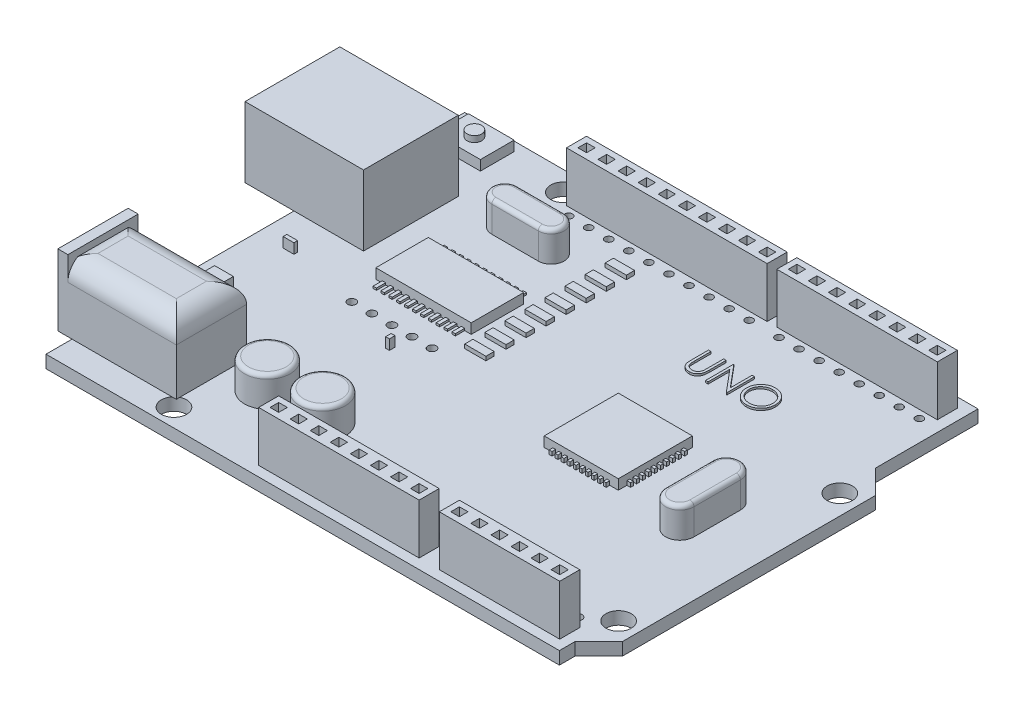
SolidWorks part; units mm, degrees
ref_plane "Front Plane" through (0, 0, 0) normal (0, 0, 1) x (1, 0, 0)
ref_plane "Top Plane" through (0, 0, 0) normal (0, 1, 0) x (1, 0, 0)
ref_plane "Right Plane" through (0, 0, 0) normal (1, 0, 0) x (0, 0, -1)
sketch "Sketch2" plane through (0, 0, 0) normal (0, 1, 0) x (1, 0, 0)
  line L0 (0, 0) -> (65, 0)
  line L1 (0, 0) -> (0, -53)
  line L2 (65, 0) -> (65, -13)
  line L3 (0, -53) -> (65, -53)
  line L4 (65, -13) -> (68, -16)
  line L5 (68, -16) -> (68, -48)
  line L6 (68, -48) -> (65, -51)
  line L7 (65, -51) -> (65, -53)
  circle A0 centre (15, -2.5) radius 1.6
  circle A1 centre (65.5, -18) radius 1.6
  circle A2 centre (65.5, -46) radius 1.6
  circle A3 centre (13.9, -50.7) radius 1.6
  dimension "D8" = 3.2
  dimension "D9" = 15
  dimension "D12" = 35
  dimension "D13" = 50.5
  dimension "D14" = 1.1
  dimension "D15" = 4.7
  dimension "D1" = 65
  dimension "D2" = 53
  dimension "D3" = 37
  dimension "D4" = 40
  dimension "D5" = 2
  dimension "D6" = 5
  dimension "D7" = 68
  dimension "D10" = 65.5
  dimension "D11" = 7
extrude "Boss-Extrude1" add sketch "Sketch2" along normal blind 1.6
sketch "Sketch3" plane through (0, 1.6, 0) normal (0, 1, 0) x (1, 0, 0)
  line L0 (-6.2, -9.6) -> (8.8, -9.6)
  line L1 (-6.2, -9.6) -> (-6.2, -21.6)
  line L2 (8.8, -9.6) -> (8.8, -21.6)
  line L3 (-6.2, -21.6) -> (8.8, -21.6)
  line L4 (65, 0) -> (0, 0) construction
  line L5 (0, 0) -> (0, -53) construction
  dimension "D1" = 9.6
  dimension "D2" = 12
  dimension "D3" = 15
  dimension "D4" = 6.2
extrude "Boss-Extrude2" add sketch "Sketch3" along normal blind 8.9
sketch "Sketch5" plane through (0, 1.6, 0) normal (0, 1, 0) x (1, 0, 0)
  line L0 (0, 0) -> (0, -9.6) construction
  line L1 (7.4283, -5.4315) -> (1.6434, -5.4315)
  line L2 (7.4283, -5.4315) -> (7.4283, -1.1571)
  line L3 (7.4283, -1.1571) -> (1.6434, -1.1571)
  line L4 (1.6434, -5.4315) -> (1.6434, -1.1571)
  line L5 (7.4283, -5.4315) -> (1.6434, -1.1571) construction
  line L6 (7.4283, -1.1571) -> (1.6434, -5.4315) construction
  line L7 (65, 0) -> (0, 0) construction
  point P0 (4.5358, -3.2943)
  dimension "D1" = 4.2744
  dimension "D2" = 5.7848
  dimension "D3" = 1.6434
  dimension "D4" = 1.1571
extrude "Boss-Extrude3" add sketch "Sketch5" along normal blind 1.27
sketch "Sketch6" plane through (0, 2.87, 0) normal (0, 1, 0) x (1, 0, 0)
  line L0 (1.6434, -1.1571) -> (7.4283, -5.4315) construction
  circle A0 centre (4.5358, -3.2943) radius 0.9278
  dimension "D1" = 1.8555
extrude "Boss-Extrude4" add sketch "Sketch6" along normal blind 0.762
sketch "Sketch7" plane through (0, 1.6, 0) normal (0, 1, 0) x (1, 0, 0)
  line L0 (0, -21.6) -> (0, -53) construction
  line L1 (-1.8, -40.8) -> (13.2, -40.8)
  line L2 (-1.8, -40.8) -> (-1.8, -49.7)
  line L3 (-1.8, -49.7) -> (13.2, -49.7)
  line L4 (13.2, -40.8) -> (13.2, -49.7)
  line L5 (-1.8, -40.8) -> (13.2, -49.7) construction
  line L6 (-1.8, -49.7) -> (13.2, -40.8) construction
  line L7 (0, -53) -> (65, -53) construction
  point P0 (5.7, -45.25)
  dimension "D1" = 8.9
  dimension "D2" = 1.8
  dimension "D3" = 15
  dimension "D4" = 3.3
extrude "Boss-Extrude5" add sketch "Sketch7" along normal blind 8.5
fillet "Fillet1" radius 2.54 4 edges at (5.7, 10.1, 49.7) (-1.8, 10.1, 45.25) (5.7, 10.1, 40.8) (13.2, 10.1, 45.25)
sketch "Sketch8" plane through (-1.8, 0, 0) normal (-1, 0, 0) x (0, 0, 1)
  line L0 (49.7, 1.6) -> (53, 1.6) construction
  line L1 (49.7, 1.6) -> (40.8, 1.6)
  line L2 (49.7, 1.6) -> (49.7, 10.6)
  line L3 (49.7, 10.6) -> (40.8, 10.6)
  line L4 (40.8, 1.6) -> (40.8, 10.6)
  line L5 (49.7, 1.6) -> (40.8, 10.6) construction
  line L6 (49.7, 10.6) -> (40.8, 1.6) construction
  line L7 (49.7, 7.56) -> (49.7, 1.6) construction
  line L9 (40.8, 7.56) -> (40.8, 1.6) construction
  point P0 (45.25, 6.1)
  dimension "D1" = 9
extrude "Boss-Extrude6" add sketch "Sketch8" against normal blind 1.27
sketch "Sketch9" plane through (-1.8, 0, 0) normal (-1, 0, 0) x (0, 0, 1)
  line L0 (45.25, 10.6) -> (45.25, 1.6) construction
  line L1 (49.7, 10.6) -> (40.8, 10.6) construction
  line L2 (40.8, 1.6) -> (49.7, 1.6) construction
  circle A0 centre (45.25, 6.1) radius 3
  dimension "D1" = 6
extrude "Cut-Extrude2" cut sketch "Sketch9" against normal blind 8.89
sketch "Sketch11" plane through (0, 1.6, 0) normal (0, 1, 0) x (1, 0, 0)
  line L0 (15.083, -10) -> (20.9573, -10) construction
  line L1 (15.083, -8.3682) -> (20.9573, -8.3682)
  line L2 (15.083, -11.6318) -> (20.9573, -11.6318)
  line L3 (59.2606, -32.0122) -> (59.2606, -26.1378) construction
  line L4 (57.4656, -32.0122) -> (57.4656, -26.1378)
  line L5 (61.0555, -32.0122) -> (61.0555, -26.1378)
  line L6 (0, -53) -> (65, -53) construction
  line L7 (0, -21.6) -> (0, -40.8) construction
  line L8 (65, 0) -> (0, 0) construction
  circle A0 centre (18.0202, -43) radius 2.8915
  circle A1 centre (25.0202, -43) radius 2.8915
  arc A2 (15.083, -8.3682) -> (15.083, -11.6318) centre (15.083, -10) ccw
  arc A3 (20.9573, -11.6318) -> (20.9573, -8.3682) centre (20.9573, -10) ccw
  arc A4 (57.4656, -32.0122) -> (61.0555, -32.0122) centre (59.2606, -32.0122) ccw
  arc A5 (61.0555, -26.1378) -> (57.4656, -26.1378) centre (59.2606, -26.1378) ccw
  point P6 (18.0202, -10)
  point P11 (59.2606, -29.075)
  dimension "D1" = 7
  dimension "D2" = 5.783
  dimension "D4" = 18.0202
  dimension "D6" = 1.6318
  dimension "14" = 10
  dimension "D5" = 5.8744
  dimension "D7" = 10
  dimension "D8" = 18.0202
extrude "Boss-Extrude8" add sketch "Sketch11" along normal blind 3.81
fillet "Fillet2" radius 0.508 1 edges at (18.0202, 5.41, 45.8915)
fillet "Fillet3" radius 0.508 9 edges at (59.2606, 5.41, 24.3429) (61.0555, 5.41, 29.075) (59.2606, 5.41, 33.8071) (18.0202, 5.41, 8.3682) (22.5891, 5.41, 10) (18.0202, 5.41, 11.6318) (57.4656, 5.41, 29.075) (13.4512, 5.41, 10) (25.0202, 5.41, 45.8915)
sketch "Sketch12" plane through (0, 1.6, 0) normal (0, 1, 0) x (1, 0, 0)
  line L0 (39.53, -1.23) -> (39.53, -3.77) construction
  line L1 (16.67, -1.23) -> (42.07, -1.23)
  line L2 (16.67, -1.23) -> (16.67, -3.77)
  line L3 (16.67, -3.77) -> (42.07, -3.77)
  line L4 (42.07, -1.23) -> (42.07, -3.77)
  line L5 (16.67, -1.23) -> (42.07, -3.77) construction
  line L6 (16.67, -3.77) -> (42.07, -1.23) construction
  line L7 (43.3, -1.23) -> (63.62, -1.23)
  line L8 (43.3, -1.23) -> (43.3, -3.77)
  line L9 (43.3, -3.77) -> (63.62, -3.77)
  line L10 (63.62, -1.23) -> (63.62, -3.77)
  line L11 (43.3, -1.23) -> (63.62, -3.77) construction
  line L12 (43.3, -3.77) -> (63.62, -1.23) construction
  line L13 (39.53, -1.23) -> (42.07, -3.77) construction
  line L14 (0, 0) -> (0, -9.6) construction
  line L15 (16.67, -2.5) -> (15, -2.5) construction
  line L17 (25.65, -49.19) -> (45.97, -49.19)
  line L18 (25.65, -49.19) -> (25.65, -51.73)
  line L19 (25.65, -51.73) -> (45.97, -51.73)
  line L20 (45.97, -49.19) -> (45.97, -51.73)
  line L21 (48.53, -49.19) -> (63.77, -49.19)
  line L22 (48.53, -49.19) -> (48.53, -51.73)
  line L23 (48.53, -51.73) -> (63.77, -51.73)
  line L24 (63.77, -49.19) -> (63.77, -51.73)
  line L25 (43.43, -49.19) -> (43.43, -51.73) construction
  line L26 (43.43, -51.73) -> (45.97, -49.19) construction
  line L27 (0, -49.7) -> (0, -53) construction
  line L28 (0, -53) -> (65, -53) construction
  line L29 (63.77, -49.19) -> (61.23, -51.73) construction
  line L30 (63.62, -1.23) -> (61.38, -3.77) construction
  circle A0 centre (15, -2.5) radius 1.6 construction
  point P0 (29.37, -2.5)
  point P5 (53.46, -2.5)
  point P14 (40.8, -2.5)
  point P27 (45.97, -50.46)
  point P28 (44.7, -50.46)
  point P35 (62.5, -50.46)
  point P37 (62.5, -2.5)
  dimension "D1" = 25.4
  dimension "D2" = 2.54
  dimension "D3" = 2.54
  dimension "D4" = 40.8
  dimension "D5" = 20.32
  dimension "D6" = 2.54
  dimension "D7" = 44.7
  dimension "D8" = 2.54
  dimension "D9" = 2.54
  dimension "D10" = 62.5
  dimension "D11" = 2.24
  dimension "D12" = 62.5
  dimension "D13" = 20.32
  dimension "D14" = 15.24
extrude "Boss-Extrude9" add sketch "Sketch12" along normal blind 6.35
sketch "Sketch13" plane through (0, 7.95, 0) normal (0, 1, 0) x (1, 0, 0)
  line L0 (19.9337, -3.0463) -> (19.9337, -1.9537)
  line L1 (18.4863, -3.0463) -> (17.3937, -3.0463)
  line L2 (18.4863, -3.0463) -> (18.4863, -1.9537)
  line L3 (18.4863, -1.9537) -> (17.3937, -1.9537)
  line L4 (17.3937, -3.0463) -> (17.3937, -1.9537)
  line L5 (18.4863, -3.0463) -> (17.3937, -1.9537) construction
  line L6 (18.4863, -1.9537) -> (17.3937, -3.0463) construction
  line L7 (21.0263, -1.9537) -> (19.9337, -1.9537)
  line L8 (21.0263, -3.0463) -> (19.9337, -3.0463)
  line L9 (21.0263, -3.0463) -> (21.0263, -1.9537)
  line L10 (22.4737, -3.0463) -> (22.4737, -1.9537)
  line L11 (23.5663, -1.9537) -> (22.4737, -1.9537)
  line L12 (23.5663, -3.0463) -> (22.4737, -3.0463)
  line L13 (23.5663, -3.0463) -> (23.5663, -1.9537)
  line L14 (25.0137, -3.0463) -> (25.0137, -1.9537)
  line L15 (26.1063, -1.9537) -> (25.0137, -1.9537)
  line L16 (26.1063, -3.0463) -> (25.0137, -3.0463)
  line L17 (26.1063, -3.0463) -> (26.1063, -1.9537)
  line L18 (27.5537, -3.0463) -> (27.5537, -1.9537)
  line L19 (28.6463, -1.9537) -> (27.5537, -1.9537)
  line L20 (28.6463, -3.0463) -> (27.5537, -3.0463)
  line L21 (28.6463, -3.0463) -> (28.6463, -1.9537)
  line L22 (30.0937, -3.0463) -> (30.0937, -1.9537)
  line L23 (31.1863, -1.9537) -> (30.0937, -1.9537)
  line L24 (31.1863, -3.0463) -> (30.0937, -3.0463)
  line L25 (31.1863, -3.0463) -> (31.1863, -1.9537)
  line L26 (32.6337, -3.0463) -> (32.6337, -1.9537)
  line L27 (33.7263, -1.9537) -> (32.6337, -1.9537)
  line L28 (33.7263, -3.0463) -> (32.6337, -3.0463)
  line L29 (33.7263, -3.0463) -> (33.7263, -1.9537)
  line L30 (35.1737, -3.0463) -> (35.1737, -1.9537)
  line L31 (36.2663, -1.9537) -> (35.1737, -1.9537)
  line L32 (36.2663, -3.0463) -> (35.1737, -3.0463)
  line L33 (36.2663, -3.0463) -> (36.2663, -1.9537)
  line L34 (16.67, -2.5) -> (17.94, -2.5) construction
  line L35 (16.67, -1.23) -> (16.67, -3.77) construction
  line L36 (42.07, -1.23) -> (43.3, -1.23) construction
  line L37 (43.3, -1.23) -> (42.685, -1.23) construction
  line L38 (42.685, -1.23) -> (42.685, 0) construction
  line L39 (65, 0) -> (0, 0) construction
  line L40 (44.0237, -3.0463) -> (44.0237, -1.9537)
  line L41 (44.0237, -3.0463) -> (45.1163, -3.0463)
  line L42 (44.0237, -1.9537) -> (45.1163, -1.9537)
  line L43 (49.1037, -3.0463) -> (49.1037, -1.9537)
  line L44 (49.1037, -3.0463) -> (50.1963, -3.0463)
  line L45 (49.1037, -1.9537) -> (50.1963, -1.9537)
  line L46 (50.1963, -3.0463) -> (50.1963, -1.9537)
  line L47 (51.6437, -3.0463) -> (51.6437, -1.9537)
  line L48 (51.6437, -3.0463) -> (52.7363, -3.0463)
  line L49 (51.6437, -1.9537) -> (52.7363, -1.9537)
  line L50 (52.7363, -3.0463) -> (52.7363, -1.9537)
  line L51 (54.1837, -3.0463) -> (54.1837, -1.9537)
  line L52 (54.1837, -3.0463) -> (55.2763, -3.0463)
  line L53 (54.1837, -1.9537) -> (55.2763, -1.9537)
  line L54 (55.2763, -3.0463) -> (55.2763, -1.9537)
  line L55 (56.7237, -3.0463) -> (56.7237, -1.9537)
  line L56 (56.7237, -3.0463) -> (57.8163, -3.0463)
  line L57 (56.7237, -1.9537) -> (57.8163, -1.9537)
  line L58 (57.8163, -3.0463) -> (57.8163, -1.9537)
  line L59 (59.2637, -3.0463) -> (59.2637, -1.9537)
  line L60 (59.2637, -3.0463) -> (60.3563, -3.0463)
  line L61 (59.2637, -1.9537) -> (60.3563, -1.9537)
  line L62 (60.3563, -3.0463) -> (60.3563, -1.9537)
  line L63 (61.8037, -3.0463) -> (61.8037, -1.9537)
  line L64 (61.8037, -3.0463) -> (62.8963, -3.0463)
  line L65 (61.8037, -1.9537) -> (62.8963, -1.9537)
  line L66 (62.8963, -3.0463) -> (62.8963, -1.9537)
  line L67 (45.1163, -3.0463) -> (45.1163, -1.9537)
  line L68 (46.5637, -3.0463) -> (46.5637, -1.9537)
  line L69 (46.5637, -3.0463) -> (47.6563, -3.0463)
  line L71 (46.5637, -1.9537) -> (47.6563, -1.9537)
  line L72 (47.6563, -3.0463) -> (47.6563, -1.9537)
  line L73 (41.6137, -49.9137) -> (42.7063, -49.9137)
  line L74 (41.6137, -49.9137) -> (41.6137, -51.0063)
  line L75 (41.6137, -51.0063) -> (42.7063, -51.0063)
  line L77 (26.3737, -49.9137) -> (27.4663, -49.9137)
  line L78 (26.3737, -49.9137) -> (26.3737, -51.0063)
  line L79 (26.3737, -51.0063) -> (27.4663, -51.0063)
  line L80 (27.4663, -49.9137) -> (27.4663, -51.0063)
  line L81 (26.3737, -50.46) -> (25.65, -50.46) construction
  line L82 (25.65, -49.19) -> (25.65, -51.73) construction
  line L83 (28.9137, -49.9137) -> (30.0063, -49.9137)
  line L84 (28.9137, -49.9137) -> (28.9137, -51.0063)
  line L85 (28.9137, -51.0063) -> (30.0063, -51.0063)
  line L86 (30.0063, -49.9137) -> (30.0063, -51.0063)
  line L87 (31.4537, -49.9137) -> (32.5463, -49.9137)
  line L88 (31.4537, -49.9137) -> (31.4537, -51.0063)
  line L89 (31.4537, -51.0063) -> (32.5463, -51.0063)
  line L90 (32.5463, -49.9137) -> (32.5463, -51.0063)
  line L91 (33.9937, -49.9137) -> (35.0863, -49.9137)
  line L92 (33.9937, -49.9137) -> (33.9937, -51.0063)
  line L93 (33.9937, -51.0063) -> (35.0863, -51.0063)
  line L94 (35.0863, -49.9137) -> (35.0863, -51.0063)
  line L95 (36.5337, -49.9137) -> (37.6263, -49.9137)
  line L96 (36.5337, -49.9137) -> (36.5337, -51.0063)
  line L97 (36.5337, -51.0063) -> (37.6263, -51.0063)
  line L98 (37.6263, -49.9137) -> (37.6263, -51.0063)
  line L99 (39.0737, -49.9137) -> (40.1663, -49.9137)
  line L100 (39.0737, -49.9137) -> (39.0737, -51.0063)
  line L101 (39.0737, -51.0063) -> (40.1663, -51.0063)
  line L102 (40.1663, -49.9137) -> (40.1663, -51.0063)
  line L103 (45.97, -51.73) -> (48.53, -51.73) construction
  line L104 (48.53, -51.73) -> (47.25, -51.73) construction
  line L105 (47.25, -51.73) -> (47.25, -53) construction
  line L106 (0, -53) -> (65, -53) construction
  line L107 (49.2537, -49.9137) -> (49.2537, -51.0063)
  line L108 (54.3337, -49.9137) -> (54.3337, -51.0063)
  line L109 (55.4263, -51.0063) -> (54.3337, -51.0063)
  line L110 (55.4263, -49.9137) -> (55.4263, -51.0063)
  line L111 (55.4263, -49.9137) -> (54.3337, -49.9137)
  line L112 (56.8737, -49.9137) -> (56.8737, -51.0063)
  line L113 (57.9663, -51.0063) -> (56.8737, -51.0063)
  line L114 (57.9663, -49.9137) -> (57.9663, -51.0063)
  line L115 (57.9663, -49.9137) -> (56.8737, -49.9137)
  line L116 (59.4137, -49.9137) -> (59.4137, -51.0063)
  line L117 (60.5063, -51.0063) -> (59.4137, -51.0063)
  line L118 (60.5063, -49.9137) -> (60.5063, -51.0063)
  line L119 (60.5063, -49.9137) -> (59.4137, -49.9137)
  line L120 (61.9537, -49.9137) -> (61.9537, -51.0063)
  line L121 (63.0463, -51.0063) -> (61.9537, -51.0063)
  line L122 (63.0463, -49.9137) -> (63.0463, -51.0063)
  line L123 (63.0463, -49.9137) -> (61.9537, -49.9137)
  line L124 (50.3463, -51.0063) -> (49.2537, -51.0063)
  line L125 (50.3463, -49.9137) -> (50.3463, -51.0063)
  line L126 (50.3463, -49.9137) -> (49.2537, -49.9137)
  line L127 (51.7937, -49.9137) -> (51.7937, -51.0063)
  line L128 (52.8863, -51.0063) -> (51.7937, -51.0063)
  line L129 (52.8863, -49.9137) -> (52.8863, -51.0063)
  line L130 (52.8863, -49.9137) -> (51.7937, -49.9137)
  line L132 (37.7137, -3.0463) -> (37.7137, -1.9537)
  line L133 (38.8063, -1.9537) -> (37.7137, -1.9537)
  line L134 (38.8063, -3.0463) -> (37.7137, -3.0463)
  line L135 (38.8063, -3.0463) -> (38.8063, -1.9537)
  line L136 (40.2537, -3.0463) -> (40.2537, -1.9537)
  line L137 (41.3463, -1.9537) -> (40.2537, -1.9537)
  line L138 (41.3463, -3.0463) -> (40.2537, -3.0463)
  line L139 (41.3463, -3.0463) -> (41.3463, -1.9537)
  line L140 (42.7063, -49.9137) -> (42.7063, -51.0063)
  line L141 (44.1537, -49.9137) -> (45.2463, -49.9137)
  line L142 (44.1537, -49.9137) -> (44.1537, -51.0063)
  line L143 (44.1537, -51.0063) -> (45.2463, -51.0063)
  line L144 (45.2463, -49.9137) -> (45.2463, -51.0063)
  point P0 (17.94, -2.5)
  point P84 (26.92, -51.0063)
  dimension "D2" = 2.54
  dimension "D3" = 1.0927
  dimension "D4" = 1.27
  dimension "D5" = 1.27
  dimension "D6" = 8
  dimension "D7" = 2.54
  dimension "D1" = 10
extrude "Cut-Extrude3" cut sketch "Sketch13" against normal blind 3.81
sketch "Sketch15" plane through (0, 1.6, 0) normal (0, 1, 0) x (1, 0, 0)
  line L0 (0, -53) -> (65, -53) construction
  line L1 (51.1538, -31.6917) -> (41.7703, -31.6917)
  line L2 (51.1538, -31.6917) -> (51.1538, -22.3083)
  line L3 (51.1538, -22.3083) -> (41.7703, -22.3083)
  line L4 (41.7703, -31.6917) -> (41.7703, -22.3083)
  line L5 (51.1538, -31.6917) -> (41.7703, -22.3083) construction
  line L6 (51.1538, -22.3083) -> (41.7703, -31.6917) construction
  line L7 (4.7493, -26.358) -> (3.3785, -26.358)
  line L8 (4.7493, -26.358) -> (4.7493, -25.8868)
  line L9 (4.7493, -25.8868) -> (3.3785, -25.8868)
  line L10 (3.3785, -26.358) -> (3.3785, -25.8868)
  line L11 (4.7493, -26.358) -> (3.3785, -25.8868) construction
  line L12 (4.7493, -25.8868) -> (3.3785, -26.358) construction
  line L13 (21.3282, -30.8535) -> (20.8488, -30.8535)
  line L14 (21.3282, -30.8535) -> (21.3282, -30.1486)
  line L15 (21.3282, -30.1486) -> (20.8488, -30.1486)
  line L16 (20.8488, -30.8535) -> (20.8488, -30.1486)
  line L17 (21.3282, -30.8535) -> (20.8488, -30.1486) construction
  line L18 (21.3282, -30.1486) -> (20.8488, -30.8535) construction
  line L19 (4.6108, -37.8097) -> (2.2268, -37.8097)
  line L20 (4.6108, -37.8097) -> (4.6108, -33.8836)
  line L21 (4.6108, -33.8836) -> (2.2268, -33.8836)
  line L22 (2.2268, -37.8097) -> (2.2268, -33.8836)
  line L23 (4.6108, -37.8097) -> (2.2268, -33.8836) construction
  line L24 (4.6108, -33.8836) -> (2.2268, -37.8097) construction
  line L25 (24.7492, -23.9138) -> (12.6715, -23.9138)
  line L26 (24.7492, -23.9138) -> (24.7492, -17.271)
  line L27 (24.7492, -17.271) -> (12.6715, -17.271)
  line L28 (12.6715, -23.9138) -> (12.6715, -17.271)
  line L29 (24.7492, -23.9138) -> (12.6715, -17.271) construction
  line L30 (24.7492, -17.271) -> (12.6715, -23.9138) construction
  line L31 (68, -48) -> (68, -16) construction
  line L32 (0, -21.6) -> (0, -40.8) construction
  line L34 (65, 0) -> (0, 0) construction
  point P0 (46.4621, -27)
  point P5 (4.0639, -26.1224)
  point P10 (21.0885, -30.501)
  point P15 (3.4188, -35.8466)
  point P20 (18.7104, -20.5924)
  dimension "D1" = 9.3835
  dimension "D2" = 12.0778
  dimension "D3" = 6.6428
  dimension "D4" = 26
  dimension "D5" = 21.5379
  dimension "D6" = 18.7104
  dimension "D7" = 20.5924
extrude "Boss-Extrude10" add sketch "Sketch15" along normal blind 1.27
sketch "Sketch16" plane through (0, 1.6, 0) normal (0, 1, 0) x (1, 0, 0)
  line L0 (17.94, -3.0463) -> (17.94, -4.77) construction
  line L1 (17.3937, -3.0463) -> (18.4863, -3.0463) construction
  line L2 (16.67, -3.77) -> (42.07, -3.77) construction
  line L3 (40.8, -3.0463) -> (40.8, -4.77) construction
  line L4 (40.2537, -3.0463) -> (41.3463, -3.0463) construction
  line L5 (42.07, -1.23) -> (43.3, -1.23) construction
  line L6 (43.3, -1.23) -> (42.685, -1.23) construction
  line L7 (42.685, -1.23) -> (42.685, 0) construction
  line L8 (65, 0) -> (0, 0) construction
  line L9 (44.57, -3.0463) -> (44.57, -4.77) construction
  circle A0 centre (-9.9058, 11.1483) radius 1.2565
  circle A1 centre (30.64, -4.77) radius 0.4778
  circle A2 centre (33.18, -4.77) radius 0.4778
  circle A3 centre (17.94, -4.77) radius 0.4778
  circle A4 centre (20.48, -4.77) radius 0.4778
  circle A5 centre (23.02, -4.77) radius 0.4778
  circle A6 centre (25.56, -4.77) radius 0.4778
  circle A7 centre (28.1, -4.77) radius 0.4778
  circle A8 centre (35.72, -4.77) radius 0.4778
  circle A9 centre (38.26, -4.77) radius 0.4778
  circle A10 centre (40.8, -4.77) radius 0.4778
  circle A11 centre (44.57, -4.77) radius 0.4778
  circle A12 centre (47.11, -4.77) radius 0.4778
  circle A13 centre (49.65, -4.77) radius 0.4778
  circle A14 centre (57.27, -4.77) radius 0.4778
  circle A15 centre (59.81, -4.77) radius 0.4778
  circle A16 centre (62.35, -4.77) radius 0.4778
  circle A19 centre (52.19, -4.77) radius 0.4778
  circle A20 centre (54.73, -4.77) radius 0.4778
  dimension "D4" = 0.9556
  dimension "D2" = 2.54
  dimension "D3" = 1
  dimension "D1" = 10
extrude "Cut-Extrude5" cut sketch "Sketch16" against normal blind 3.81
sketch "Sketch17" plane through (0, 1.6, 0) normal (0, 1, 0) x (1, 0, 0)
  line L0 (28.5824, -23.3444) -> (25.9009, -22.3015) construction
  line L1 (28.5824, -25.8844) -> (25.9009, -25.8844)
  line L2 (28.5824, -25.8844) -> (28.5824, -24.8415)
  line L3 (28.5824, -24.8415) -> (25.9009, -24.8415)
  line L4 (25.9009, -25.8844) -> (25.9009, -24.8415)
  line L5 (28.5824, -25.8844) -> (25.9009, -24.8415) construction
  line L6 (28.5824, -24.8415) -> (25.9009, -25.8844) construction
  line L7 (28.5824, -22.3015) -> (25.9009, -23.3444) construction
  line L8 (28.5824, -23.3444) -> (28.5824, -22.3015)
  line L9 (28.5824, -23.3444) -> (25.9009, -23.3444)
  line L10 (25.9009, -23.3444) -> (25.9009, -22.3015)
  line L11 (28.5824, -22.3015) -> (25.9009, -22.3015)
  line L12 (28.5824, -20.8044) -> (25.9009, -19.7615) construction
  line L13 (28.5824, -19.7615) -> (25.9009, -20.8044) construction
  line L14 (28.5824, -20.8044) -> (28.5824, -19.7615)
  line L15 (28.5824, -20.8044) -> (25.9009, -20.8044)
  line L16 (25.9009, -20.8044) -> (25.9009, -19.7615)
  line L17 (28.5824, -19.7615) -> (25.9009, -19.7615)
  line L18 (28.5824, -18.2644) -> (25.9009, -17.2215) construction
  line L19 (28.5824, -17.2215) -> (25.9009, -18.2644) construction
  line L20 (28.5824, -18.2644) -> (28.5824, -17.2215)
  line L21 (28.5824, -18.2644) -> (25.9009, -18.2644)
  line L22 (25.9009, -18.2644) -> (25.9009, -17.2215)
  line L23 (28.5824, -17.2215) -> (25.9009, -17.2215)
  line L24 (28.5824, -15.7244) -> (25.9009, -14.6815) construction
  line L25 (28.5824, -14.6815) -> (25.9009, -15.7244) construction
  line L26 (28.5824, -15.7244) -> (28.5824, -14.6815)
  line L27 (28.5824, -15.7244) -> (25.9009, -15.7244)
  line L28 (25.9009, -15.7244) -> (25.9009, -14.6815)
  line L29 (28.5824, -14.6815) -> (25.9009, -14.6815)
  line L30 (28.5824, -13.1844) -> (25.9009, -12.1415) construction
  line L31 (28.5824, -12.1415) -> (25.9009, -13.1844) construction
  line L32 (28.5824, -13.1844) -> (28.5824, -12.1415)
  line L33 (28.5824, -13.1844) -> (25.9009, -13.1844)
  line L34 (25.9009, -13.1844) -> (25.9009, -12.1415)
  line L35 (28.5824, -12.1415) -> (25.9009, -12.1415)
  line L36 (28.5824, -10.6444) -> (25.9009, -9.6015) construction
  line L37 (28.5824, -9.6015) -> (25.9009, -10.6444) construction
  line L38 (28.5824, -10.6444) -> (28.5824, -9.6015)
  line L39 (28.5824, -10.6444) -> (25.9009, -10.6444)
  line L40 (25.9009, -10.6444) -> (25.9009, -9.6015)
  line L41 (28.5824, -9.6015) -> (25.9009, -9.6015)
  line L42 (28.5824, -8.1044) -> (25.9009, -7.0615) construction
  line L43 (28.5824, -7.0615) -> (25.9009, -8.1044) construction
  line L44 (28.5824, -8.1044) -> (28.5824, -7.0615)
  line L45 (28.5824, -8.1044) -> (25.9009, -8.1044)
  line L46 (25.9009, -8.1044) -> (25.9009, -7.0615)
  line L47 (28.5824, -7.0615) -> (25.9009, -7.0615)
  point P0 (27.2416, -25.363)
  point P6 (27.2416, -22.823)
  point P12 (27.2416, -20.283)
  point P17 (27.2416, -17.743)
  point P22 (27.2416, -15.203)
  point P27 (27.2416, -12.663)
  point P32 (27.2416, -10.123)
  point P37 (27.2416, -7.583)
  dimension "D2" = 1.0429
  dimension "D3" = 2.54
  dimension "D1" = 8
extrude "Boss-Extrude11" add sketch "Sketch17" along normal blind 0.508
sketch "Sketch18" plane through (0, 1.6, 0) normal (0, 1, 0) x (1, 0, 0)
  text T0 "UNO"
sketch "Sketch20" plane through (0, 1.6, 0) normal (0, 1, 0) x (1, 0, 0)
  line L0 (45.97, -49.19) -> (25.65, -49.19) construction
  line L1 (26.92, -48.19) -> (26.92, -49.9137) construction
  line L2 (27.4663, -49.9137) -> (26.3737, -49.9137) construction
  line L3 (45.97, -51.73) -> (48.53, -51.73) construction
  line L4 (48.53, -51.73) -> (47.25, -51.73) construction
  line L5 (47.25, -51.73) -> (47.25, -53) construction
  line L6 (0, -53) -> (65, -53) construction
  circle A0 centre (26.92, -48.19) radius 0.5676
  circle A1 centre (29.46, -48.19) radius 0.5676
  circle A2 centre (32, -48.19) radius 0.5676
  circle A3 centre (34.54, -48.19) radius 0.5676
  circle A4 centre (37.08, -48.19) radius 0.5676
  circle A5 centre (39.62, -48.19) radius 0.5676
  circle A6 centre (42.16, -48.19) radius 0.5676
  circle A7 centre (44.7, -48.19) radius 0.5676
  circle A8 centre (49.8, -48.19) radius 0.5676
  circle A9 centre (52.34, -48.19) radius 0.5676
  circle A10 centre (54.88, -48.19) radius 0.5676
  circle A11 centre (57.42, -48.19) radius 0.5676
  circle A12 centre (59.96, -48.19) radius 0.5676
  circle A13 centre (62.5, -48.19) radius 0.5676
  dimension "D1" = 8
  dimension "D2" = 1.1352
  dimension "D3" = 2.54
  dimension "D4" = 1
extrude "Cut-Extrude6" cut sketch "Sketch20" against normal blind 23.368
sketch "Sketch21" plane through (0, 1.6, 0) normal (0, 1, 0) x (1, 0, 0)
  line L0 (18.7104, -23.9138) -> (18.7104, -27.9138) construction
  line L1 (12.6715, -23.9138) -> (24.7492, -23.9138) construction
  circle A0 centre (13.6304, -27.9138) radius 0.5282
  circle A1 centre (16.1704, -27.9138) radius 0.5282
  circle A2 centre (18.7104, -27.9138) radius 0.5282
  circle A3 centre (21.2504, -27.9138) radius 0.5282
  circle A4 centre (23.7904, -27.9138) radius 0.5282
  dimension "D1" = 5
  dimension "D3" = 1.0565
  dimension "D2" = 2.54
  dimension "D4" = 4
extrude "Cut-Extrude7" cut sketch "Sketch21" against normal blind 13.208
sketch "Sketch22" plane through (0, 1.6, 0) normal (0, 1, 0) x (1, 0, 0)
  line L0 (41.7703, -31.6917) -> (51.1538, -31.6917) construction
  line L1 (42.857, -31.2344) -> (43.2091, -31.2344)
  line L2 (42.857, -31.2344) -> (42.857, -32.149)
  line L3 (42.857, -32.149) -> (43.2091, -32.149)
  line L4 (43.2091, -31.2344) -> (43.2091, -32.149)
  line L5 (42.857, -31.2344) -> (43.2091, -32.149) construction
  line L6 (42.857, -32.149) -> (43.2091, -31.2344) construction
  line L7 (43.619, -31.2344) -> (43.9711, -32.149) construction
  line L8 (43.619, -32.149) -> (43.9711, -31.2344) construction
  line L9 (43.619, -31.2344) -> (43.619, -32.149)
  line L10 (43.619, -31.2344) -> (43.9711, -31.2344)
  line L11 (43.9711, -31.2344) -> (43.9711, -32.149)
  line L12 (43.619, -32.149) -> (43.9711, -32.149)
  line L13 (44.381, -31.2344) -> (44.7331, -32.149) construction
  line L14 (44.381, -32.149) -> (44.7331, -31.2344) construction
  line L15 (44.381, -31.2344) -> (44.381, -32.149)
  line L16 (44.381, -31.2344) -> (44.7331, -31.2344)
  line L17 (44.7331, -31.2344) -> (44.7331, -32.149)
  line L18 (44.381, -32.149) -> (44.7331, -32.149)
  line L19 (45.143, -31.2344) -> (45.4951, -32.149) construction
  line L20 (45.143, -32.149) -> (45.4951, -31.2344) construction
  line L21 (45.143, -31.2344) -> (45.143, -32.149)
  line L22 (45.143, -31.2344) -> (45.4951, -31.2344)
  line L23 (45.4951, -31.2344) -> (45.4951, -32.149)
  line L24 (45.143, -32.149) -> (45.4951, -32.149)
  line L25 (45.905, -31.2344) -> (46.2571, -32.149) construction
  line L26 (45.905, -32.149) -> (46.2571, -31.2344) construction
  line L27 (45.905, -31.2344) -> (45.905, -32.149)
  line L28 (45.905, -31.2344) -> (46.2571, -31.2344)
  line L29 (46.2571, -31.2344) -> (46.2571, -32.149)
  line L30 (45.905, -32.149) -> (46.2571, -32.149)
  line L31 (46.667, -31.2344) -> (47.0191, -32.149) construction
  line L32 (46.667, -32.149) -> (47.0191, -31.2344) construction
  line L33 (46.667, -31.2344) -> (46.667, -32.149)
  line L34 (46.667, -31.2344) -> (47.0191, -31.2344)
  line L35 (47.0191, -31.2344) -> (47.0191, -32.149)
  line L36 (46.667, -32.149) -> (47.0191, -32.149)
  line L37 (47.429, -31.2344) -> (47.7811, -32.149) construction
  line L38 (47.429, -32.149) -> (47.7811, -31.2344) construction
  line L39 (47.429, -31.2344) -> (47.429, -32.149)
  line L40 (47.429, -31.2344) -> (47.7811, -31.2344)
  line L41 (47.7811, -31.2344) -> (47.7811, -32.149)
  line L42 (47.429, -32.149) -> (47.7811, -32.149)
  line L43 (48.191, -31.2344) -> (48.5431, -32.149) construction
  line L44 (48.191, -32.149) -> (48.5431, -31.2344) construction
  line L45 (48.191, -31.2344) -> (48.191, -32.149)
  line L46 (48.191, -31.2344) -> (48.5431, -31.2344)
  line L47 (48.5431, -31.2344) -> (48.5431, -32.149)
  line L48 (48.191, -32.149) -> (48.5431, -32.149)
  line L49 (48.953, -31.2344) -> (49.3051, -32.149) construction
  line L50 (48.953, -32.149) -> (49.3051, -31.2344) construction
  line L51 (48.953, -31.2344) -> (48.953, -32.149)
  line L52 (48.953, -31.2344) -> (49.3051, -31.2344)
  line L53 (49.3051, -31.2344) -> (49.3051, -32.149)
  line L54 (48.953, -32.149) -> (49.3051, -32.149)
  line L55 (49.715, -31.2344) -> (50.0671, -32.149) construction
  line L56 (49.715, -32.149) -> (50.0671, -31.2344) construction
  line L57 (49.715, -31.2344) -> (49.715, -32.149)
  line L58 (49.715, -31.2344) -> (50.0671, -31.2344)
  line L59 (50.0671, -31.2344) -> (50.0671, -32.149)
  line L60 (49.715, -32.149) -> (50.0671, -32.149)
  line L61 (46.4621, -31.6917) -> (46.4621, -22.3083) construction
  line L62 (41.7703, -31.6917) -> (51.1538, -31.6917) construction
  line L63 (51.1538, -22.3083) -> (41.7703, -22.3083) construction
  line L64 (46.4621, -27) -> (41.7703, -27) construction
  line L65 (41.7703, -22.3083) -> (41.7703, -31.6917) construction
  line L66 (42.2276, -23.3949) -> (42.2276, -23.7471)
  line L67 (42.2276, -23.3949) -> (41.313, -23.3949)
  line L68 (42.2276, -23.7471) -> (41.313, -23.7471)
  line L69 (41.313, -23.3949) -> (41.313, -23.7471)
  line L70 (42.2276, -24.1569) -> (41.313, -24.1569)
  line L71 (42.2276, -24.1569) -> (42.2276, -24.5091)
  line L72 (42.2276, -24.5091) -> (41.313, -24.5091)
  line L73 (42.2276, -24.9189) -> (42.2276, -25.2711)
  line L74 (42.2276, -25.2711) -> (41.313, -25.2711)
  line L75 (42.2276, -24.9189) -> (41.313, -24.9189)
  line L76 (41.313, -24.1569) -> (41.313, -24.5091)
  line L77 (41.313, -24.9189) -> (41.313, -25.2711)
  line L78 (42.2276, -25.6809) -> (42.2276, -26.0331)
  line L79 (42.2276, -25.6809) -> (41.313, -25.6809)
  line L80 (42.2276, -26.0331) -> (41.313, -26.0331)
  line L81 (41.313, -25.6809) -> (41.313, -26.0331)
  line L82 (42.2276, -26.4429) -> (41.313, -26.4429)
  line L83 (42.2276, -26.4429) -> (42.2276, -26.7951)
  line L84 (42.2276, -26.7951) -> (41.313, -26.7951)
  line L85 (42.2276, -27.2049) -> (41.313, -27.2049)
  line L86 (42.2276, -27.2049) -> (42.2276, -27.5571)
  line L87 (42.2276, -27.5571) -> (41.313, -27.5571)
  line L88 (41.313, -27.2049) -> (41.313, -27.5571)
  line L89 (41.313, -26.4429) -> (41.313, -26.7951)
  line L90 (42.2276, -27.9669) -> (42.2276, -28.3191)
  line L91 (42.2276, -27.9669) -> (41.313, -27.9669)
  line L92 (41.313, -27.9669) -> (41.313, -28.3191)
  line L93 (42.2276, -28.7289) -> (41.313, -28.7289)
  line L94 (42.2276, -28.3191) -> (41.313, -28.3191)
  line L95 (42.2276, -28.7289) -> (42.2276, -29.0811)
  line L96 (42.2276, -29.0811) -> (41.313, -29.0811)
  line L97 (41.313, -28.7289) -> (41.313, -29.0811)
  line L98 (42.2276, -29.4909) -> (42.2276, -29.8431)
  line L99 (42.2276, -29.4909) -> (41.313, -29.4909)
  line L100 (42.2276, -29.8431) -> (41.313, -29.8431)
  line L101 (41.313, -29.4909) -> (41.313, -29.8431)
  line L102 (42.2276, -30.2529) -> (41.313, -30.2529)
  line L103 (42.2276, -30.2529) -> (42.2276, -30.6051)
  line L104 (42.2276, -30.6051) -> (41.313, -30.6051)
  line L105 (41.313, -30.2529) -> (41.313, -30.6051)
  line L106 (50.0671, -22.7656) -> (49.715, -22.7656)
  line L107 (50.0671, -22.7656) -> (50.0671, -21.851)
  line L108 (49.715, -22.7656) -> (49.715, -21.851)
  line L109 (50.0671, -21.851) -> (49.715, -21.851)
  line L110 (49.3051, -22.7656) -> (49.3051, -21.851)
  line L111 (49.3051, -22.7656) -> (48.953, -22.7656)
  line L112 (48.953, -22.7656) -> (48.953, -21.851)
  line L113 (48.5431, -22.7656) -> (48.191, -22.7656)
  line L114 (48.191, -22.7656) -> (48.191, -21.851)
  line L115 (48.5431, -22.7656) -> (48.5431, -21.851)
  line L116 (49.3051, -21.851) -> (48.953, -21.851)
  line L117 (48.5431, -21.851) -> (48.191, -21.851)
  line L118 (47.7811, -22.7656) -> (47.429, -22.7656)
  line L119 (47.7811, -22.7656) -> (47.7811, -21.851)
  line L120 (47.429, -22.7656) -> (47.429, -21.851)
  line L121 (47.7811, -21.851) -> (47.429, -21.851)
  line L122 (47.0191, -22.7656) -> (47.0191, -21.851)
  line L123 (47.0191, -22.7656) -> (46.667, -22.7656)
  line L124 (46.667, -22.7656) -> (46.667, -21.851)
  line L125 (46.2571, -22.7656) -> (46.2571, -21.851)
  line L126 (46.2571, -22.7656) -> (45.905, -22.7656)
  line L127 (45.905, -22.7656) -> (45.905, -21.851)
  line L128 (46.2571, -21.851) -> (45.905, -21.851)
  line L129 (47.0191, -21.851) -> (46.667, -21.851)
  line L130 (45.4951, -22.7656) -> (45.143, -22.7656)
  line L131 (45.4951, -22.7656) -> (45.4951, -21.851)
  line L132 (45.4951, -21.851) -> (45.143, -21.851)
  line L133 (44.7331, -22.7656) -> (44.7331, -21.851)
  line L134 (45.143, -22.7656) -> (45.143, -21.851)
  line L135 (44.7331, -22.7656) -> (44.381, -22.7656)
  line L136 (44.381, -22.7656) -> (44.381, -21.851)
  line L137 (44.7331, -21.851) -> (44.381, -21.851)
  line L138 (43.9711, -22.7656) -> (43.619, -22.7656)
  line L139 (43.9711, -22.7656) -> (43.9711, -21.851)
  line L140 (43.619, -22.7656) -> (43.619, -21.851)
  line L141 (43.9711, -21.851) -> (43.619, -21.851)
  line L142 (43.2091, -22.7656) -> (43.2091, -21.851)
  line L143 (43.2091, -22.7656) -> (42.857, -22.7656)
  line L144 (42.857, -22.7656) -> (42.857, -21.851)
  line L145 (43.2091, -21.851) -> (42.857, -21.851)
  line L146 (50.6965, -30.6051) -> (50.6965, -30.2529)
  line L147 (50.6965, -30.6051) -> (51.6111, -30.6051)
  line L148 (50.6965, -30.2529) -> (51.6111, -30.2529)
  line L149 (51.6111, -30.6051) -> (51.6111, -30.2529)
  line L150 (50.6965, -29.8431) -> (51.6111, -29.8431)
  line L151 (50.6965, -29.8431) -> (50.6965, -29.4909)
  line L152 (50.6965, -29.4909) -> (51.6111, -29.4909)
  line L153 (50.6965, -29.0811) -> (50.6965, -28.7289)
  line L154 (50.6965, -28.7289) -> (51.6111, -28.7289)
  line L155 (50.6965, -29.0811) -> (51.6111, -29.0811)
  line L156 (51.6111, -29.8431) -> (51.6111, -29.4909)
  line L157 (51.6111, -29.0811) -> (51.6111, -28.7289)
  line L158 (50.6965, -28.3191) -> (50.6965, -27.9669)
  line L159 (50.6965, -28.3191) -> (51.6111, -28.3191)
  line L160 (50.6965, -27.9669) -> (51.6111, -27.9669)
  line L161 (51.6111, -28.3191) -> (51.6111, -27.9669)
  line L162 (50.6965, -27.5571) -> (51.6111, -27.5571)
  line L163 (50.6965, -27.5571) -> (50.6965, -27.2049)
  line L164 (50.6965, -27.2049) -> (51.6111, -27.2049)
  line L165 (50.6965, -26.7951) -> (51.6111, -26.7951)
  line L166 (50.6965, -26.7951) -> (50.6965, -26.4429)
  line L167 (50.6965, -26.4429) -> (51.6111, -26.4429)
  line L168 (51.6111, -26.7951) -> (51.6111, -26.4429)
  line L169 (51.6111, -27.5571) -> (51.6111, -27.2049)
  line L170 (50.6965, -26.0331) -> (50.6965, -25.6809)
  line L171 (50.6965, -26.0331) -> (51.6111, -26.0331)
  line L172 (51.6111, -26.0331) -> (51.6111, -25.6809)
  line L173 (50.6965, -25.2711) -> (51.6111, -25.2711)
  line L174 (50.6965, -25.6809) -> (51.6111, -25.6809)
  line L175 (50.6965, -25.2711) -> (50.6965, -24.9189)
  line L176 (50.6965, -24.9189) -> (51.6111, -24.9189)
  line L177 (51.6111, -25.2711) -> (51.6111, -24.9189)
  line L178 (50.6965, -24.5091) -> (50.6965, -24.1569)
  line L179 (50.6965, -24.5091) -> (51.6111, -24.5091)
  line L180 (50.6965, -24.1569) -> (51.6111, -24.1569)
  line L181 (51.6111, -24.5091) -> (51.6111, -24.1569)
  line L182 (50.6965, -23.7471) -> (51.6111, -23.7471)
  line L183 (50.6965, -23.7471) -> (50.6965, -23.3949)
  line L184 (50.6965, -23.3949) -> (51.6111, -23.3949)
  line L185 (51.6111, -23.7471) -> (51.6111, -23.3949)
  line L186 (42.857, -21.851) -> (43.2091, -22.7656) construction
  point P0 (43.0331, -31.6917)
  point P7 (43.0331, -22.3083)
  point P9 (43.7951, -31.6917)
  point P14 (44.5571, -31.6917)
  point P19 (45.3191, -31.6917)
  point P24 (46.0811, -31.6917)
  point P29 (46.8431, -31.6917)
  point P34 (47.6051, -31.6917)
  point P39 (48.3671, -31.6917)
  point P44 (49.1291, -31.6917)
  point P49 (49.8911, -31.6917)
  dimension "D1" = 10
  dimension "D2" = 0.3521
  dimension "D3" = 0.9146
  dimension "D4" = 0.762
  dimension "D5" = 4
extrude "Boss-Extrude12" add sketch "Sketch22" along normal blind 0.508
extrude "Boss-Extrude14" add sketch "Sketch18" along normal blind 0.254
sketch "Sketch25" plane through (0, 1.6, 0) normal (0, 1, 0) x (1, 0, 0)
  line L0 (14.4975, -25.0924) -> (14.4975, -16.0924)
  line L1 (13.9232, -25.0924) -> (13.4975, -25.0924)
  line L2 (13.9232, -25.0924) -> (13.9232, -16.0924)
  line L3 (13.9232, -16.0924) -> (13.4975, -16.0924)
  line L4 (13.4975, -25.0924) -> (13.4975, -16.0924)
  line L5 (13.9232, -25.0924) -> (13.4975, -16.0924) construction
  line L6 (13.9232, -16.0924) -> (13.4975, -25.0924) construction
  line L7 (14.9232, -16.0924) -> (14.4975, -16.0924)
  line L8 (14.9232, -25.0924) -> (14.9232, -16.0924)
  line L9 (14.9232, -25.0924) -> (14.4975, -25.0924)
  line L10 (15.4975, -25.0924) -> (15.4975, -16.0924)
  line L11 (15.9232, -16.0924) -> (15.4975, -16.0924)
  line L12 (15.9232, -25.0924) -> (15.9232, -16.0924)
  line L13 (15.9232, -25.0924) -> (15.4975, -25.0924)
  line L14 (16.4975, -25.0924) -> (16.4975, -16.0924)
  line L15 (16.9232, -16.0924) -> (16.4975, -16.0924)
  line L16 (16.9232, -25.0924) -> (16.9232, -16.0924)
  line L17 (16.9232, -25.0924) -> (16.4975, -25.0924)
  line L18 (17.4975, -25.0924) -> (17.4975, -16.0924)
  line L19 (17.9232, -16.0924) -> (17.4975, -16.0924)
  line L20 (17.9232, -25.0924) -> (17.9232, -16.0924)
  line L21 (17.9232, -25.0924) -> (17.4975, -25.0924)
  line L22 (18.4975, -25.0924) -> (18.4975, -16.0924)
  line L23 (18.9232, -16.0924) -> (18.4975, -16.0924)
  line L24 (18.9232, -25.0924) -> (18.9232, -16.0924)
  line L25 (18.9232, -25.0924) -> (18.4975, -25.0924)
  line L26 (19.4975, -25.0924) -> (19.4975, -16.0924)
  line L27 (19.9232, -16.0924) -> (19.4975, -16.0924)
  line L28 (19.9232, -25.0924) -> (19.9232, -16.0924)
  line L29 (19.9232, -25.0924) -> (19.4975, -25.0924)
  line L30 (20.4975, -25.0924) -> (20.4975, -16.0924)
  line L31 (20.9232, -16.0924) -> (20.4975, -16.0924)
  line L32 (20.9232, -25.0924) -> (20.9232, -16.0924)
  line L33 (20.9232, -25.0924) -> (20.4975, -25.0924)
  line L34 (21.4975, -25.0924) -> (21.4975, -16.0924)
  line L35 (21.9232, -16.0924) -> (21.4975, -16.0924)
  line L36 (21.9232, -25.0924) -> (21.9232, -16.0924)
  line L37 (21.9232, -25.0924) -> (21.4975, -25.0924)
  line L38 (22.4975, -25.0924) -> (22.4975, -16.0924)
  line L39 (22.9232, -16.0924) -> (22.4975, -16.0924)
  line L40 (22.9232, -25.0924) -> (22.9232, -16.0924)
  line L41 (22.9232, -25.0924) -> (22.4975, -25.0924)
  line L42 (23.4975, -25.0924) -> (23.4975, -16.0924)
  line L43 (23.9232, -16.0924) -> (23.4975, -16.0924)
  line L44 (23.9232, -25.0924) -> (23.9232, -16.0924)
  line L45 (23.9232, -25.0924) -> (23.4975, -25.0924)
  line L46 (12.6715, -20.5924) -> (13.4975, -20.5924) construction
  line L47 (12.6715, -17.271) -> (12.6715, -23.9138) construction
  line L48 (24.7492, -20.5924) -> (23.9232, -20.5924) construction
  line L49 (24.7492, -23.9138) -> (24.7492, -17.271) construction
  point P0 (13.7104, -20.5924)
  dimension "D1" = 11
  dimension "D2" = 9
  dimension "D3" = 0.4257
  dimension "D4" = 1
extrude "Boss-Extrude15" add sketch "Sketch25" along normal blind 0.254
sketch "Sketch26" plane through (-6.2, 0, 0) normal (-1, 0, 0) x (0, 0, 1)
  line L0 (10.6, 2.6) -> (10.6, 7.5)
  line L1 (10.6, 7.5) -> (12.6, 9.5)
  line L2 (12.6, 9.5) -> (18.6, 9.5)
  line L3 (18.6, 9.5) -> (20.6, 7.5)
  line L4 (20.6, 7.5) -> (20.6, 2.6)
  line L5 (20.6, 2.6) -> (10.6, 2.6)
  line L6 (15.6, 10.5) -> (15.6, 1.6) construction
  line L7 (13.6, 6.5) -> (17.6, 6.5)
  line L8 (13.6, 6.5) -> (13.6, 5)
  line L9 (13.6, 5) -> (17.6, 5)
  line L10 (17.6, 6.5) -> (17.6, 5)
  line L11 (9.6, 10.5) -> (21.6, 10.5) construction
  line L12 (9.6, 1.6) -> (21.6, 1.6) construction
  line L13 (9.6, 10.5) -> (9.6, 1.6) construction
  point P16 (13.5055, 9.5041)
  point P17 (9.9566, -2.3984)
  point P18 (0, 0)
  point P19 (12.5228, 8.7943)
  point P20 (13.6693, 8.4667)
  point P23 (10.6, 7.4293)
  point P24 (0, 0)
  point P25 (13.0142, 9.5)
  point P26 (10.6, 7.4839)
  point P27 (20.6, 2.6247)
  dimension "D1" = 1
  dimension "D2" = 1
  dimension "D3" = 6
  dimension "D4" = 1
  dimension "D5" = 45
  dimension "D6" = 1.5
  dimension "4" = 4
  dimension "D7" = 3
extrude "Cut-Extrude8" cut sketch "Sketch26" against normal blind 12
